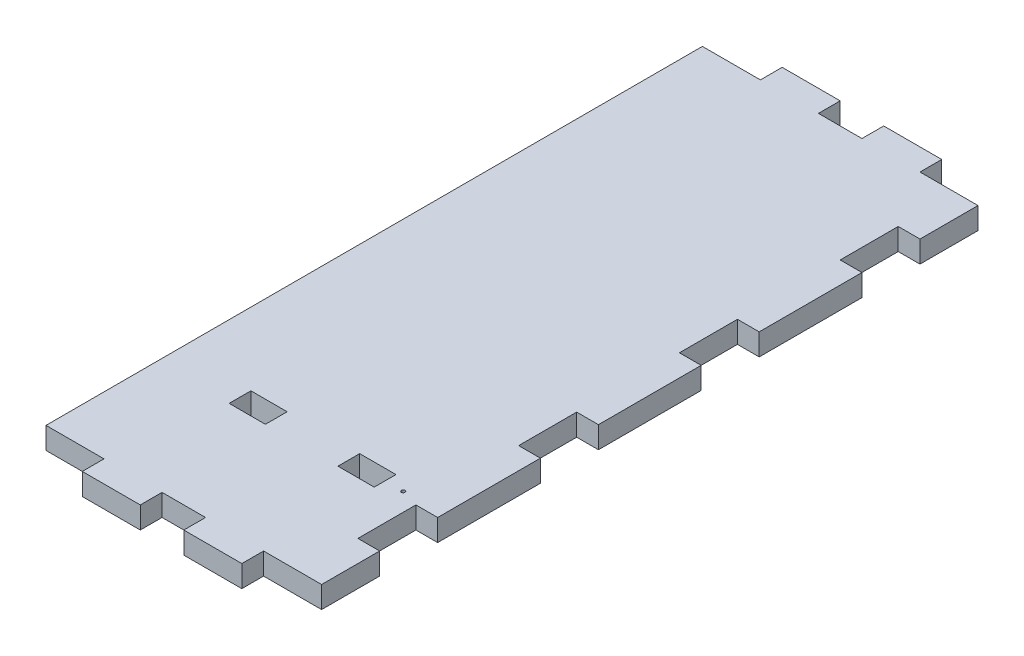
SolidWorks part; units mm, degrees
ref_plane "Front Plane" through (0, 0, 0) normal (0, 0, 1) x (1, 0, 0)
ref_plane "Top Plane" through (0, 0, 0) normal (0, 1, 0) x (1, 0, 0)
ref_plane "Right Plane" through (0, 0, 0) normal (1, 0, 0) x (0, 0, -1)
sketch "Sketch1" plane through (0, 0, 0) normal (0, 1, 0) x (1, 0, 0)
  line L0 (-25, 96.5) -> (-25, -96.5)
  line L1 (-35, 96.5) -> (35, 96.5)
  line L2 (-35, 96.5) -> (-35, -96.5)
  line L3 (-35, -96.5) -> (35, -96.5)
  line L4 (35, 96.5) -> (35, -96.5)
  line L5 (-35, 96.5) -> (35, -96.5) construction
  line L6 (-35, -96.5) -> (35, 96.5) construction
  point P0 (0, 0)
sketch "Sketch2" plane through (0, 0, 0) normal (0, 0, 1) x (1, 0, 0)
  line L0 (0, 0) -> (0, 6) construction
  line L1 (-35, 0) -> (35, 0) construction
extrude "Boss-Extrude1" add sketch "Sketch1" along normal up to vertex (6 mm away) contours L4 L1 L0 L3 | L2 L3 L0 L1 up to point (0, 6, 0)
sketch "Sketch4" plane through (0, 6, 0) normal (0, 1, 0) x (1, 0, 0)
  line L0 (35, 96.5) -> (35, -96.5) construction
  line L1 (35, 96.5) -> (35, -96.5)
  line L2 (35, 96.5) -> (41, 96.5)
  line L3 (41, 96.5) -> (41, -96.5)
  line L4 (41, -96.5) -> (35, -96.5)
extrude "Boss-Extrude2" add sketch "Sketch4" against normal up to surface (6 mm away) up to face at (0, 0, 0)
sketch "Sketch5" plane through (0, 6, 0) normal (0, 1, 0) x (1, 0, 0)
  line L0 (-35, -90.5) -> (35, -90.5) construction
  line L2 (-35, 96.5) -> (-35, -96.5) construction
  line L3 (35, -90.5) -> (35, 0) construction
  line L5 (35, 0) -> (41, 0) construction
  line L6 (41, -96.5) -> (41, 96.5) construction
  line L7 (-35, -90.5) -> (-35, -96.5) construction
  line L8 (38, -58.5) -> (38, -30.1667) construction
  line L9 (35, -74.5) -> (41, -74.5)
  line L10 (35, -74.5) -> (35, -58.5)
  line L11 (35, -58.5) -> (41, -58.5)
  line L12 (41, -74.5) -> (41, -58.5)
  line L13 (35, -14.1667) -> (41, -14.1667)
  line L14 (35, -14.1667) -> (35, -30.1667)
  line L15 (35, -30.1667) -> (41, -30.1667)
  line L16 (41, -14.1667) -> (41, -30.1667)
  line L17 (38, -14.1667) -> (38, 14.1667)
  line L18 (-35, -96.5) -> (41, -96.5) construction
  line L19 (41, -96.5) -> (25, -96.5)
  line L20 (41, -96.5) -> (41, -90.5)
  line L21 (41, -90.5) -> (25, -90.5)
  line L22 (25, -96.5) -> (25, -90.5)
  line L23 (-35, -90.5) -> (-19, -90.5)
  line L24 (-35, -90.5) -> (-35, -96.5)
  line L25 (-35, -96.5) -> (-19, -96.5)
  line L26 (-19, -90.5) -> (-19, -96.5)
  line L28 (-19, -96.5) -> (-3, -96.5)
  line L29 (-19, -96.5) -> (-19, -90.5)
  line L30 (-19, -90.5) -> (-3, -90.5)
  line L31 (-3, -96.5) -> (-3, -90.5)
  line L32 (25, -90.5) -> (9, -90.5)
  line L33 (25, -90.5) -> (25, -96.5)
  line L34 (25, -96.5) -> (9, -96.5)
  line L35 (9, -90.5) -> (9, -96.5)
  line L36 (-3, -90.5) -> (9, -90.5)
  line L37 (-3, -90.5) -> (-3, -96.5)
  line L38 (-3, -96.5) -> (9, -96.5)
  line L39 (9, -90.5) -> (9, -96.5)
  point P23 (38, 0)
  line M10 (-35, -96.5) -> (41, -96.5)
  line M11 (41, -96.5) -> (41, 96.5)
  line M13 (-35, 96.5) -> (-35, -96.5)
extrude "Cut-Extrude1" cut sketch "Sketch5" against normal through all contours L11 L10 L9 M11 | L14 L15 L13 M11 | L22 L21 M10 M11 | L26 L23 M13 M10 | L36 L31 L35 M10
mirror "Mirror1" about plane through (0, 0, 0) normal (0, 0, 1) of "Cut-Extrude1"
sketch "Sketch6" plane through (0, 6, 0) normal (0, 1, 0) x (1, 0, 0)
  line L0 (25, -57) -> (35, -57) construction
  line L1 (25, -60) -> (15, -60)
  line L2 (25, -60) -> (25, -54)
  line L3 (25, -54) -> (15, -54)
  line L4 (15, -60) -> (15, -54)
  line L5 (-5, -60) -> (-15, -60)
  line L6 (-5, -60) -> (-5, -54)
  line L7 (-5, -54) -> (-15, -54)
  line L8 (-15, -60) -> (-15, -54)
  line L9 (35, -74.5) -> (35, -58.5) construction
  circle A0 centre (30, -57) radius 0.5
  dimension "D1" = 1
extrude "Cut-Extrude2" cut sketch "Sketch6" against normal through all
sketch "Sketch9" plane through (0, 6, 0) normal (0, 1, 0) x (1, 0, 0)
  text T0 "Parameters: \r\n\r\nglass:\r\nheight = 101.00\r\nwidth = 152.00\r\nthickness = 2.50\r\n\r\nwood \r\nthickness = 6.00" font "Century Gothic" height 4
equation "\"glass_width\"= 181"
equation "\"glass_height\"= 151"
equation "\"glass_thickness\"= 2.5"
equation "\"brood_space\"= 42"
equation "\"t1\"= 6"
equation "\"t2\"= 6"
equation "\"box_depth\"= \"brood_space\" + \"glass_thickness\" + \"glass_thickness\" + \"t2\" + \"t2\""
equation "\"box_width\"= \"glass_width\" + \"t1\" + \"t1\""
equation "\"food_height\"= 70"
equation "\"box_height\"= \"glass_height\" + ( \"t1\" * 3 ) + \"food_height\""
equation "\"D1@Sketch2\"=\"t1\""
equation "\"D1@Sketch1\"=\"food_height\""
equation "\"D2@Sketch1\"=\"box_width\""
equation "\"D1@Sketch4\"=\"t1\""
equation "\"D1@Sketch5\"=\"t1\""
equation "\"entry_height\"= 24"
equation "\"entry_diameter\"= 8"
equation "\"food_top_clearance\"= 10"
equation "\"bar_width\"= 20"
equation "\"glassblocker_lower_height\"= 10"
equation "\"lower_edge_stickout\"=6"
